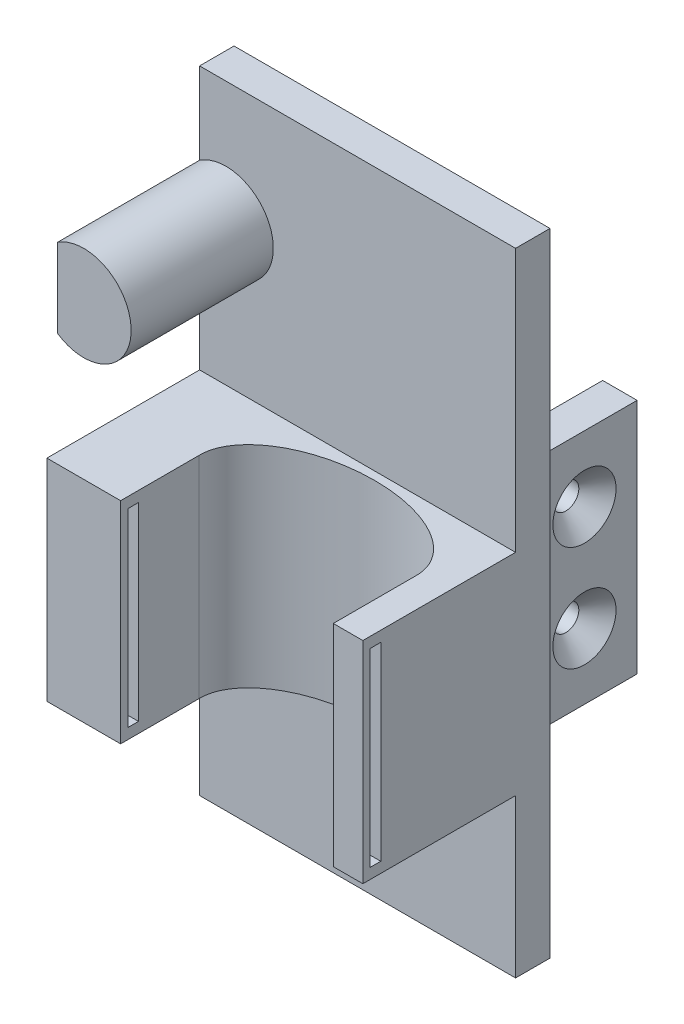
SolidWorks part; units mm, degrees
ref_plane "Front Plane" through (0, 0, 0) normal (0, 0, 1) x (1, 0, 0)
ref_plane "Top Plane" through (0, 0, 0) normal (0, 1, 0) x (1, 0, 0)
ref_plane "Right Plane" through (0, 0, 0) normal (1, 0, 0) x (0, 0, -1)
sketch "Sketch1" plane through (0, 0, 0) normal (0, 0, 1) x (1, 0, 0)
  line L1 (-30, 60) -> (30, 60)
  line L2 (-30, 60) -> (-30, -60)
  line L3 (-30, -60) -> (30, -60)
  line L4 (30, 60) -> (30, -60)
  line L5 (-30, 60) -> (30, -60) construction
  line L6 (-30, -60) -> (30, 60) construction
  point P0 (0, 0)
  dimension "D1" = 60
  dimension "D2" = 120
extrude "Boss-Extrude1" add sketch "Sketch1" along normal blind 6.54
sketch "Sketch7" plane through (0, 0, 6.54) normal (0, 0, 1) x (1, 0, 0)
  line L0 (-30, 60) -> (-30, -60) construction
  line L1 (30, 60) -> (-30, 60) construction
  line L2 (30, -60) -> (30, 60) construction
  line L7 (30, -60) -> (30, 60)
  line L8 (30, 60) -> (-30, 60)
  line L9 (-30, 60) -> (-30, -60)
  line L10 (-30, -60) -> (30, -60)
  line L13 (-30, 44.4833) -> (-30, 29.5167)
  arc A0 (-30, 29.5167) -> (-30, 44.4833) centre (-25, 37) ccw
  dimension "D1" = 9
  dimension "D2" = 23
  dimension "D3" = 55
  dimension "D4" = 0
extrude "Boss-Extrude4" add sketch "Sketch7" along normal blind 27 contours A0 L13
sketch "Sketch10" plane through (0, 0, 0) normal (0, 0, -1) x (-1, 0, 0)
  line L1 (20, 20) -> (26.54, 20)
  line L2 (-20, -25) -> (-20, 20)
  line L4 (-20, 20) -> (-26.54, 20)
  line L7 (20, -25) -> (20, 20)
  line L10 (-26.54, 20) -> (-26.54, -25)
  line L11 (-26.54, -25) -> (-20, -25)
  line L12 (26.54, 20) -> (26.54, -25)
  line L13 (26.54, -25) -> (20, -25)
  dimension "D1" = 6.54
  dimension "D2" = 20
  dimension "D3" = 6.54
  dimension "D4" = 20
  dimension "D5" = 45
  dimension "D6" = 45
extrude "Boss-Extrude5" add sketch "Sketch10" along normal blind 20
sketch "Sketch17" plane through (0, 0, 6.54) normal (0, 0, 1) x (1, 0, 0)
  line L0 (-30, 29.5167) -> (-30, -60) construction
  line L1 (-30, 10) -> (30, 10)
  line L2 (-30, 10) -> (-30, -30)
  line L3 (-30, -30) -> (30, -30)
  line L4 (30, 10) -> (30, -30)
  line L5 (30, -60) -> (30, 60) construction
  line L6 (-30, -60) -> (30, -60) construction
  line L7 (30, 60) -> (-30, 60) construction
  dimension "D1" = 40
  dimension "D2" = 30
  dimension "D3" = 50
extrude "Boss-Extrude6" add sketch "Sketch17" along normal blind 29
sketch "Sketch18" plane through (0, 10, 0) normal (0, 1, 0) x (1, 0, 0)
  line L1 (30, -35.54) -> (30, -6.54) construction
  line L2 (30, -35.54) -> (-30, -35.54) construction
  ellipse E0 centre (4.1927, -20.0963) end of major axis (24.3853, -19.5516) minor radius 12
  dimension "D1" = 46
  dimension "D2" = 5.6147
  dimension "D3" = 3.448
extrude "Cut-Extrude1" cut sketch "Sketch18" against normal up to next contours E0
sketch "Sketch21" plane through (0, 0, 35.54) normal (0, 0, 1) x (1, 0, 0)
  line L0 (30, 10) -> (-30, 10) construction
  line L1 (-16, 10) -> (24.3853, 10)
  line L2 (-16, 10) -> (-16, -30)
  line L3 (-16, -30) -> (24.3853, -30)
  line L4 (24.3853, 10) -> (24.3853, -30)
  line L5 (-30, -30) -> (30, -30) construction
  line L6 (30, -30) -> (30, 10) construction
  dimension "D1" = 5.6147
  dimension "D2" = 46
extrude "Cut-Extrude2" cut sketch "Sketch21" against normal up to next contours L2 L3 L4 L1
sketch "Sketch23" plane through (-16, 0, 0) normal (1, 0, 0) x (0, 0, -1)
  line L0 (-35.54, 10) -> (-35.54, -30) construction
  line L1 (-34.14, 8) -> (-32.14, 8)
  line L2 (-34.14, 8) -> (-34.14, -28)
  line L3 (-34.14, -28) -> (-32.14, -28)
  line L4 (-32.14, 8) -> (-32.14, -28)
  line L5 (-20.641, -30) -> (-35.54, -30) construction
  line L6 (-20.641, 10) -> (-35.54, 10) construction
  dimension "D1" = 3.4
  dimension "D2" = 2
  dimension "D3" = 2
  dimension "D4" = 2
  dimension "D5" = 36
extrude "Cut-Extrude3" cut sketch "Sketch23" against normal blind 9
sketch "Sketch24" plane through (24.3853, 0, 0) normal (-1, 0, 0) x (0, 0, 1)
  line L0 (19.9362, -30) -> (35.54, -30) construction
  line L1 (32.14, 8) -> (34.14, 8)
  line L2 (32.14, 8) -> (32.14, -28)
  line L3 (32.14, -28) -> (34.14, -28)
  line L4 (34.14, 8) -> (34.14, -28)
  line L5 (19.9362, 10) -> (35.54, 10) construction
  line L6 (35.54, 10) -> (35.54, -30) construction
  dimension "D1" = 2
  dimension "D2" = 2
  dimension "D3" = 2
  dimension "D4" = 3.4
extrude "Cut-Extrude4" cut sketch "Sketch24" against normal blind 9
hole_wizard "CSK for M3 Flat Head Machine Screw4" positions "3DSketch2" profile "Sketch27" countersink size "M3" standard "ANSI Metric" end condition up to next
sketch3d "3DSketch2"
  line L4 (26.54, -25, -20) -> (26.54, -25, 0) construction
  line L5 (26.54, 20, -20) -> (26.54, -25, -20) construction
  line L6 (26.54, 20, -20) -> (26.54, 20, 0) construction
  point P14 (26.54, -12.5, -10)
  point P26 (26.54, 7.5, -10)
  dimension "D1" = 10
  dimension "D2" = 12.5
  dimension "D3" = 12.5
  dimension "D4" = 10
sketch "Sketch27" plane through (26.54, -12.5, -10) normal (0, 1, 0) x (0, 0, -1)
  line L0 (0, 0) -> (0, 6.54)
  line L1 (0, 6.54) -> (2.465, 6.54)
  line L2 (2.465, 6.54) -> (2.465, 3.535)
  line L3 (2.465, 3.535) -> (6, 0)
  line L5 (6, 0) -> (0, 0)
  line L6 (-2.465, 3.535) -> (-6, 0) construction
  line L11 (0, -6.35) -> (0, 107.95) construction
  dimension "Thru Hole Dia." = 4.93
  dimension "Thru Hole Depth" = 6.54
  dimension "Near C'Sink Dia." = 12
  dimension "Near C'Sink Angle" = 90
hole_wizard "CSK for M3 Flat Head Machine Screw5" positions "3DSketch3" profile "Sketch29" countersink size "M3" standard "ANSI Metric" end condition up to next
sketch3d "3DSketch3"
  line L0 (-26.54, -25, -20) -> (-26.54, 20, -20) construction
  line L2 (-26.54, 20, -20) -> (-26.54, 20, 0) construction
  line L3 (-26.54, -25, -20) -> (-26.54, -25, 0) construction
  point P10 (-26.54, -12.5, -10)
  point P13 (-26.54, 7.5, -10)
  point P16 (0, 0, 0)
  dimension "D1" = 10
  dimension "D3" = 12.5
  dimension "D2" = 10
  dimension "D4" = 12.5
sketch "Sketch29" plane through (-26.54, -12.5, -10) normal (0, 1, 0) x (0, 0, 1)
  line L0 (0, 0) -> (0, 6.54)
  line L1 (0, 6.54) -> (2.465, 6.54)
  line L2 (2.465, 6.54) -> (2.465, 3.535)
  line L3 (2.465, 3.535) -> (6, 0)
  line L5 (6, 0) -> (0, 0)
  line L6 (-2.465, 3.535) -> (-6, 0) construction
  line L11 (0, -6.35) -> (0, 107.95) construction
  dimension "Thru Hole Dia." = 4.93
  dimension "Thru Hole Depth" = 6.54
  dimension "Near C'Sink Dia." = 12
  dimension "Near C'Sink Angle" = 90
